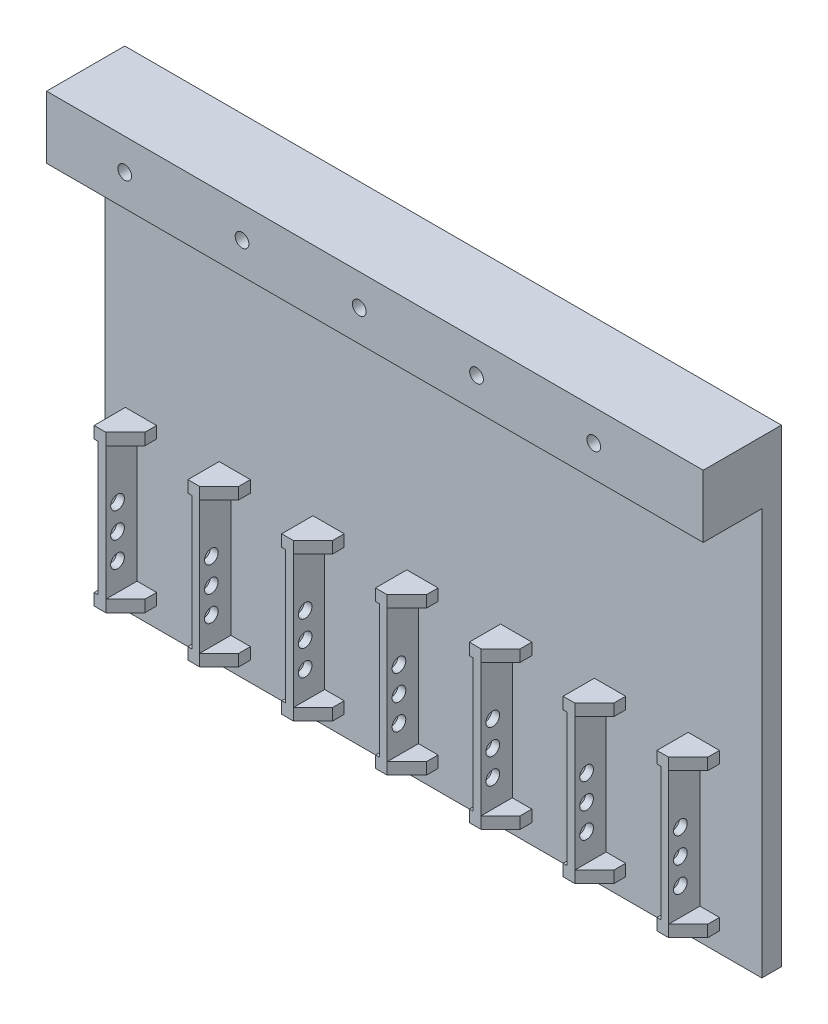
SolidWorks part; units mm, degrees
ref_plane "Front Plane" through (0, 0, 0) normal (0, 0, 1) x (1, 0, 0)
ref_plane "Top Plane" through (0, 0, 0) normal (0, 1, 0) x (1, 0, 0)
ref_plane "Right Plane" through (0, 0, 0) normal (1, 0, 0) x (0, 0, -1)
sketch "Sketch1" plane through (0, 0, 0) normal (0, 0, 1) x (1, 0, 0)
  line L1 (-84, 60) -> (84, 60)
  line L2 (-84, 60) -> (-84, -60)
  line L3 (-84, -60) -> (84, -60)
  line L4 (84, 60) -> (84, -60)
  line L5 (-84, 60) -> (84, -60) construction
  line L6 (-84, -60) -> (84, 60) construction
  point P0 (0, 0)
  dimension "D1" = 120
  dimension "D2" = 168
extrude "Boss-Extrude1" add sketch "Sketch1" along normal blind 20
sketch "Sketch2" plane through (0, 0, 20) normal (0, 0, 1) x (1, 0, 0)
  line L0 (-84, 60) -> (-84, -60) construction
  line L1 (-84, 44) -> (84, 44)
  line L2 (-84, 44) -> (-84, -60)
  line L3 (-84, -60) -> (84, -60)
  line L4 (84, 44) -> (84, -60)
  line L5 (84, -60) -> (84, 60) construction
  line L6 (-84, -60) -> (84, -60) construction
  line L7 (84, 60) -> (-84, 60) construction
  dimension "D1" = 16
extrude "Cut-Extrude1" cut sketch "Sketch2" against normal blind 15
sketch "Sketch3" plane through (0, 0, 20) normal (0, 0, 1) x (1, 0, 0)
  line L0 (84, 60) -> (-84, 60) construction
  line L1 (-84, 60) -> (-84, 44) construction
  circle A0 centre (-64, 52) radius 1.75
  circle A1 centre (-34, 52) radius 1.75
  circle A2 centre (-4, 52) radius 1.75
  circle A3 centre (26, 52) radius 1.75
  circle A4 centre (56, 52) radius 1.75
  dimension "D3" = 3.5
  dimension "D1" = 8
  dimension "D2" = 20
  dimension "D4" = 5
extrude "Cut-Extrude2" cut sketch "Sketch3" against normal through all
sketch "Sketch5" plane through (0, 0, 5) normal (0, 0, 1) x (1, 0, 0)
  line L1 (-75.85, -55) -> (-77.85, -55)
  line L2 (-75.85, -55) -> (-75.85, -15)
  line L3 (-75.85, -15) -> (-77.85, -15)
  line L4 (-77.85, -55) -> (-77.85, -15)
  line L6 (-84, 44) -> (-84, -60) construction
  line L7 (-84, -60) -> (84, -60) construction
  dimension "D1" = 2
  dimension "D2" = 6.15
  dimension "D3" = 5
  dimension "D4" = 40
extrude "Boss-Extrude2" add sketch "Sketch5" along normal blind 8
sketch "Sketch6" plane through (-77.85, 0, 0) normal (-1, 0, 0) x (0, 0, 1)
  line L0 (13, -55) -> (5, -55) construction
  line L1 (13, -15) -> (13, -55) construction
  circle A0 centre (10, -45) radius 1.75
  circle A1 centre (10, -38.5) radius 1.75
  circle A2 centre (10, -32) radius 1.75
  dimension "D2" = 3.5
  dimension "D1" = 10
  dimension "D3" = 3
  dimension "D4" = 3
extrude "Cut-Extrude3" cut sketch "Sketch6" against normal through all
sketch "Sketch7" plane through (0, 0, 5) normal (0, 0, 1) x (1, 0, 0)
  line L0 (-77.85, -15) -> (-77.85, -55) construction
  line L1 (-78.85, -55) -> (-70.85, -55)
  line L2 (-78.85, -55) -> (-78.85, -52)
  line L3 (-78.85, -52) -> (-70.85, -52)
  line L4 (-70.85, -55) -> (-70.85, -52)
  line L5 (-77.85, -15) -> (-77.85, -55) construction
  line L6 (-78.85, -15) -> (-70.85, -15)
  line L7 (-78.85, -15) -> (-78.85, -18)
  line L8 (-78.85, -18) -> (-70.85, -18)
  line L9 (-70.85, -15) -> (-70.85, -18)
  dimension "D1" = 8
  dimension "D2" = 1
  dimension "D3" = 3
  dimension "D4" = 8
  dimension "D5" = 3
  dimension "D6" = 1
extrude "Boss-Extrude3" add sketch "Sketch7" along normal blind 8
chamfer "Chamfer1" distance 5 angle 45 2 edges at (-70.85, -16.5, 13) (-70.85, -53.5, 13)
pattern_linear "LPattern1" count 7 spacing 24 along (1, 0, 0) of "Boss-Extrude3", "Boss-Extrude2", "Cut-Extrude3", "Chamfer1"
